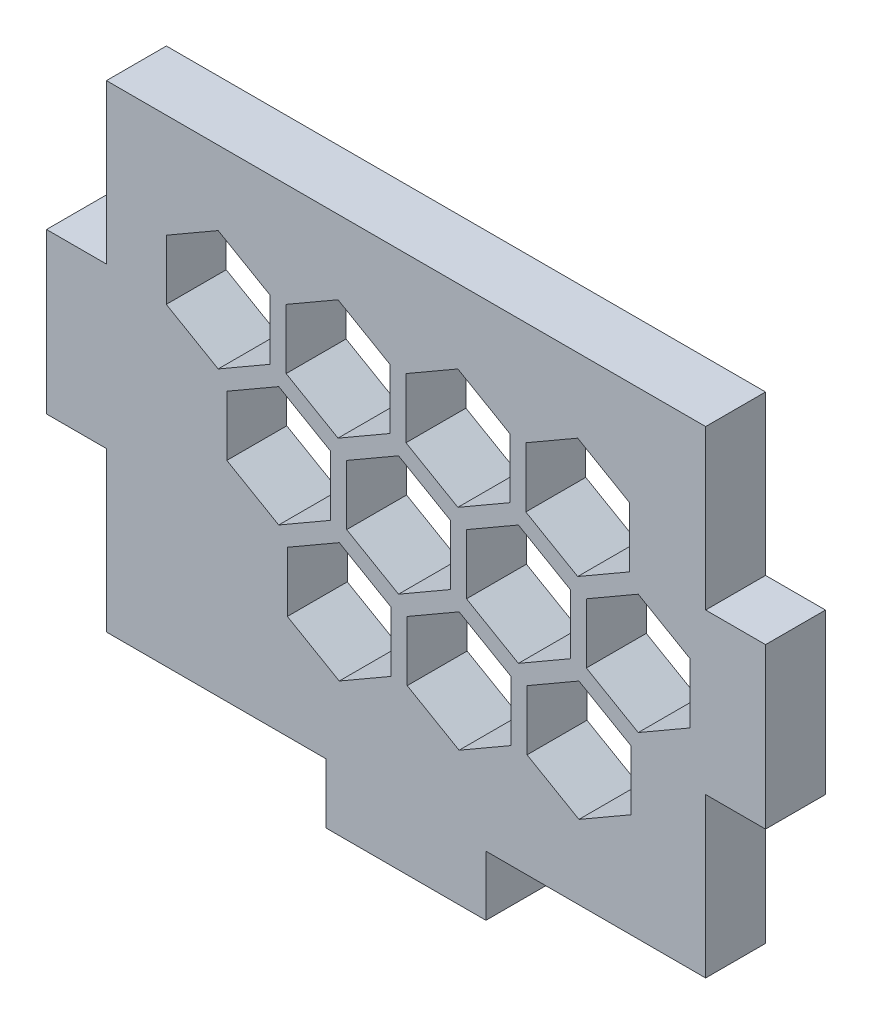
SolidWorks part; units mm, degrees
ref_plane "前视基准面" through (0, 0, 0) normal (0, 0, 1) x (1, 0, 0)
ref_plane "上视基准面" through (0, 0, 0) normal (0, 1, 0) x (1, 0, 0)
ref_plane "右视基准面" through (0, 0, 0) normal (1, 0, 0) x (0, 0, -1)
sketch "草图1" plane through (0, 0, 0) normal (0, 0, 1) x (1, 0, 0)
  line L0 (2696.1491, 1909.1565) -> (2696.1491, 1917.1115)
  line L1 (2696.1491, 1917.1115) -> (2707.1491, 1917.1115)
  line L2 (2715.1491, 1917.1115) -> (2726.1491, 1917.1115)
  line L3 (2726.1491, 1917.1115) -> (2726.1491, 1909.1565)
  line L4 (2726.1491, 1901.1565) -> (2726.1491, 1893.2015)
  line L5 (2726.1491, 1893.2015) -> (2715.1491, 1893.2015)
  line L6 (2707.1491, 1893.2015) -> (2696.1491, 1893.2015)
  line L7 (2696.1491, 1893.2015) -> (2696.1491, 1901.1565)
  line L8 (2715.1491, 1893.2015) -> (2715.1491, 1890.2015)
  line L9 (2715.1491, 1890.2015) -> (2707.1491, 1890.2015)
  line L10 (2707.1491, 1890.2015) -> (2707.1491, 1893.2015)
  line L11 (2696.1491, 1901.1565) -> (2693.1491, 1901.1565)
  line L12 (2693.1491, 1901.1565) -> (2693.1491, 1909.1565)
  line L13 (2693.1491, 1909.1565) -> (2696.1491, 1909.1565)
  line L14 (2726.1491, 1901.1565) -> (2729.1491, 1901.1565)
  line L15 (2729.1491, 1901.1565) -> (2729.1491, 1909.1565)
  line L16 (2729.1491, 1909.1565) -> (2726.1491, 1909.1565)
  line L17 (2699.1454, 1908.9065) -> (2701.7435, 1907.4065)
  line L18 (2701.7435, 1907.4065) -> (2704.3416, 1908.9065)
  line L19 (2704.3416, 1908.9065) -> (2704.3416, 1911.9065)
  line L20 (2704.3416, 1911.9065) -> (2701.7435, 1913.4065)
  line L21 (2701.7435, 1913.4065) -> (2699.1454, 1911.9065)
  line L22 (2699.1454, 1911.9065) -> (2699.1454, 1908.9065)
  line L23 (2705.1454, 1908.9065) -> (2707.7435, 1907.4065)
  line L24 (2707.7435, 1907.4065) -> (2710.3416, 1908.9065)
  line L25 (2710.3416, 1908.9065) -> (2710.3416, 1911.9065)
  line L26 (2710.3416, 1911.9065) -> (2707.7435, 1913.4065)
  line L27 (2707.7435, 1913.4065) -> (2705.1454, 1911.9065)
  line L28 (2705.1454, 1911.9065) -> (2705.1454, 1908.9065)
  line L29 (2711.1454, 1908.9065) -> (2713.7435, 1907.4065)
  line L30 (2713.7435, 1907.4065) -> (2716.3416, 1908.9065)
  line L31 (2716.3416, 1908.9065) -> (2716.3416, 1911.9065)
  line L32 (2716.3416, 1911.9065) -> (2713.7435, 1913.4065)
  line L33 (2713.7435, 1913.4065) -> (2711.1454, 1911.9065)
  line L34 (2711.1454, 1911.9065) -> (2711.1454, 1908.9065)
  line L35 (2717.1454, 1908.9065) -> (2719.7435, 1907.4065)
  line L36 (2719.7435, 1907.4065) -> (2722.3416, 1908.9065)
  line L37 (2722.3416, 1908.9065) -> (2722.3416, 1911.9065)
  line L38 (2722.3416, 1911.9065) -> (2719.7435, 1913.4065)
  line L39 (2719.7435, 1913.4065) -> (2717.1454, 1911.9065)
  line L40 (2717.1454, 1911.9065) -> (2717.1454, 1908.9065)
  line L41 (2702.1765, 1903.6565) -> (2704.7746, 1902.1565)
  line L42 (2704.7746, 1902.1565) -> (2707.3727, 1903.6565)
  line L43 (2707.3727, 1903.6565) -> (2707.3727, 1906.6565)
  line L44 (2707.3727, 1906.6565) -> (2704.7746, 1908.1565)
  line L45 (2704.7746, 1908.1565) -> (2702.1765, 1906.6565)
  line L46 (2702.1765, 1906.6565) -> (2702.1765, 1903.6565)
  line L47 (2708.1765, 1903.6565) -> (2710.7746, 1902.1565)
  line L48 (2710.7746, 1902.1565) -> (2713.3727, 1903.6565)
  line L49 (2713.3727, 1903.6565) -> (2713.3727, 1906.6565)
  line L50 (2713.3727, 1906.6565) -> (2710.7746, 1908.1565)
  line L51 (2710.7746, 1908.1565) -> (2708.1765, 1906.6565)
  line L52 (2708.1765, 1906.6565) -> (2708.1765, 1903.6565)
  line L53 (2714.1765, 1903.6565) -> (2716.7746, 1902.1565)
  line L54 (2716.7746, 1902.1565) -> (2719.3727, 1903.6565)
  line L55 (2719.3727, 1903.6565) -> (2719.3727, 1906.6565)
  line L56 (2719.3727, 1906.6565) -> (2716.7746, 1908.1565)
  line L57 (2716.7746, 1908.1565) -> (2714.1765, 1906.6565)
  line L58 (2714.1765, 1906.6565) -> (2714.1765, 1903.6565)
  line L59 (2720.1765, 1903.6565) -> (2722.7746, 1902.1565)
  line L60 (2722.7746, 1902.1565) -> (2725.3727, 1903.6565)
  line L61 (2725.3727, 1903.6565) -> (2725.3727, 1906.6565)
  line L62 (2725.3727, 1906.6565) -> (2722.7746, 1908.1565)
  line L63 (2722.7746, 1908.1565) -> (2720.1765, 1906.6565)
  line L64 (2720.1765, 1906.6565) -> (2720.1765, 1903.6565)
  line L65 (2705.2076, 1898.4065) -> (2707.8057, 1896.9065)
  line L66 (2707.8057, 1896.9065) -> (2710.4038, 1898.4065)
  line L67 (2710.4038, 1898.4065) -> (2710.4038, 1901.4065)
  line L68 (2710.4038, 1901.4065) -> (2707.8057, 1902.9065)
  line L69 (2707.8057, 1902.9065) -> (2705.2076, 1901.4065)
  line L70 (2705.2076, 1901.4065) -> (2705.2076, 1898.4065)
  line L71 (2711.2076, 1898.4065) -> (2713.8057, 1896.9065)
  line L72 (2713.8057, 1896.9065) -> (2716.4038, 1898.4065)
  line L73 (2716.4038, 1898.4065) -> (2716.4038, 1901.4065)
  line L74 (2716.4038, 1901.4065) -> (2713.8057, 1902.9065)
  line L75 (2713.8057, 1902.9065) -> (2711.2076, 1901.4065)
  line L76 (2711.2076, 1901.4065) -> (2711.2076, 1898.4065)
  line L77 (2717.2076, 1898.4065) -> (2719.8057, 1896.9065)
  line L78 (2719.8057, 1896.9065) -> (2722.4038, 1898.4065)
  line L79 (2722.4038, 1898.4065) -> (2722.4038, 1901.4065)
  line L80 (2722.4038, 1901.4065) -> (2719.8057, 1902.9065)
  line L81 (2719.8057, 1902.9065) -> (2717.2076, 1901.4065)
  line L82 (2717.2076, 1901.4065) -> (2717.2076, 1898.4065)
  line L83 (2707.1491, 1917.1115) -> (2715.1491, 1917.1115)
extrude "凸台-拉伸1" add sketch "草图1" along normal blind 3
